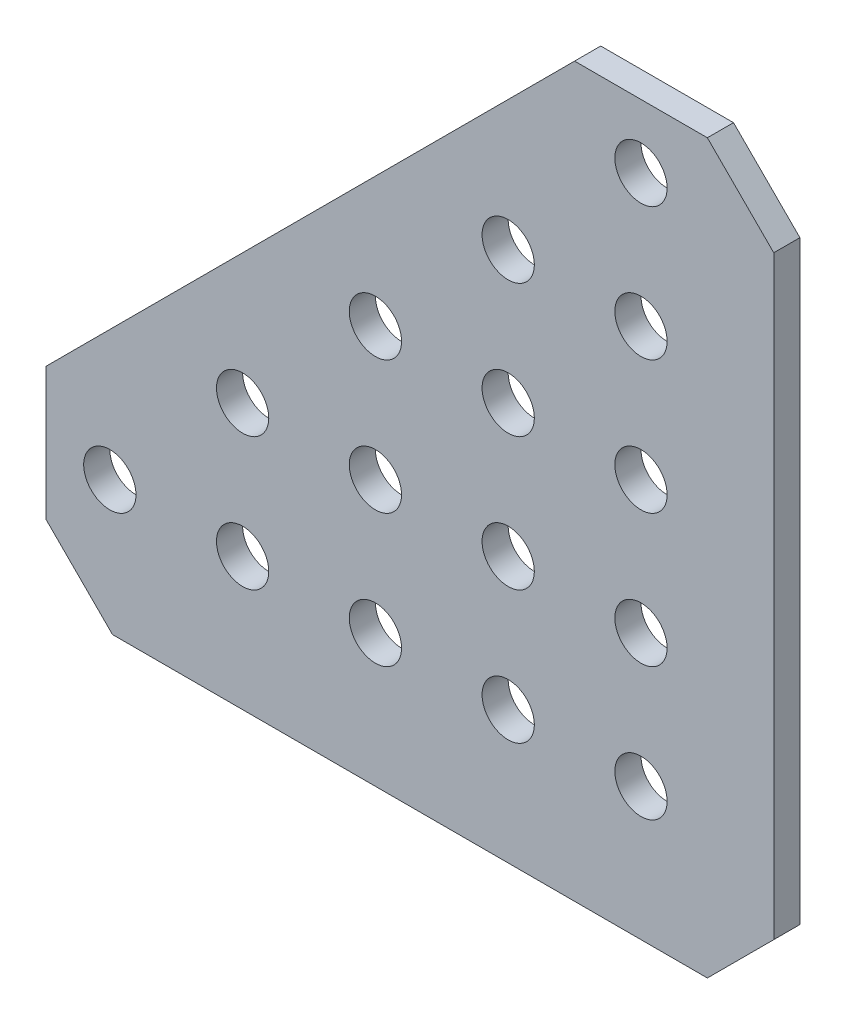
SolidWorks part; units mm, degrees
material "5052-H32"
ref_plane "Front Plane" through (0, 0, 0) normal (0, 0, 1) x (1, 0, 0)
ref_plane "Top Plane" through (0, 0, 0) normal (0, 1, 0) x (1, 0, 0)
ref_plane "Right Plane" through (0, 0, 0) normal (1, 0, 0) x (0, 0, -1)
ref_plane "Plane1" through (0, 0, -1.25) normal (0, 0, -1) x (-1, 0, 0)
sketch "Sketch1" plane through (0, 0, -1.25) normal (0, 0, -1) x (-1, 0, 0)
  line L0 (-6.35, -12.7) -> (50.546, -12.7)
  line L1 (50.546, -12.7) -> (56.896, -6.35)
  line L2 (56.896, -6.35) -> (56.896, 6.35)
  line L3 (56.896, 6.35) -> (6.35, 56.896)
  line L4 (6.35, 56.896) -> (-6.35, 56.896)
  line L5 (-6.35, 56.896) -> (-12.7, 50.546)
  line L6 (-12.7, 50.546) -> (-12.7, -6.35)
  line L7 (-12.7, -6.35) -> (-6.35, -12.7)
  circle A0 centre (0, 12.7) radius 2.5
  circle A1 centre (0, 25.4) radius 2.5
  circle A2 centre (12.7, 0) radius 2.5
  circle A3 centre (25.4, 0) radius 2.5
  circle A4 centre (0, 0) radius 2.5
  circle A5 centre (50.8, 0) radius 2.5
  circle A6 centre (38.1, 0) radius 2.5
  circle A7 centre (0, 50.8) radius 2.5
  circle A8 centre (0, 38.1) radius 2.5
  circle A9 centre (12.7, 12.7) radius 2.5
  circle A10 centre (12.7, 25.4) radius 2.5
  circle A11 centre (12.7, 38.1) radius 2.5
  circle A12 centre (25.4, 12.7) radius 2.5
  circle A13 centre (25.4, 25.4) radius 2.5
  circle A14 centre (38.1, 12.7) radius 2.5
extrude "Boss-Extrude1" add sketch "Sketch1" against normal blind 2.5
